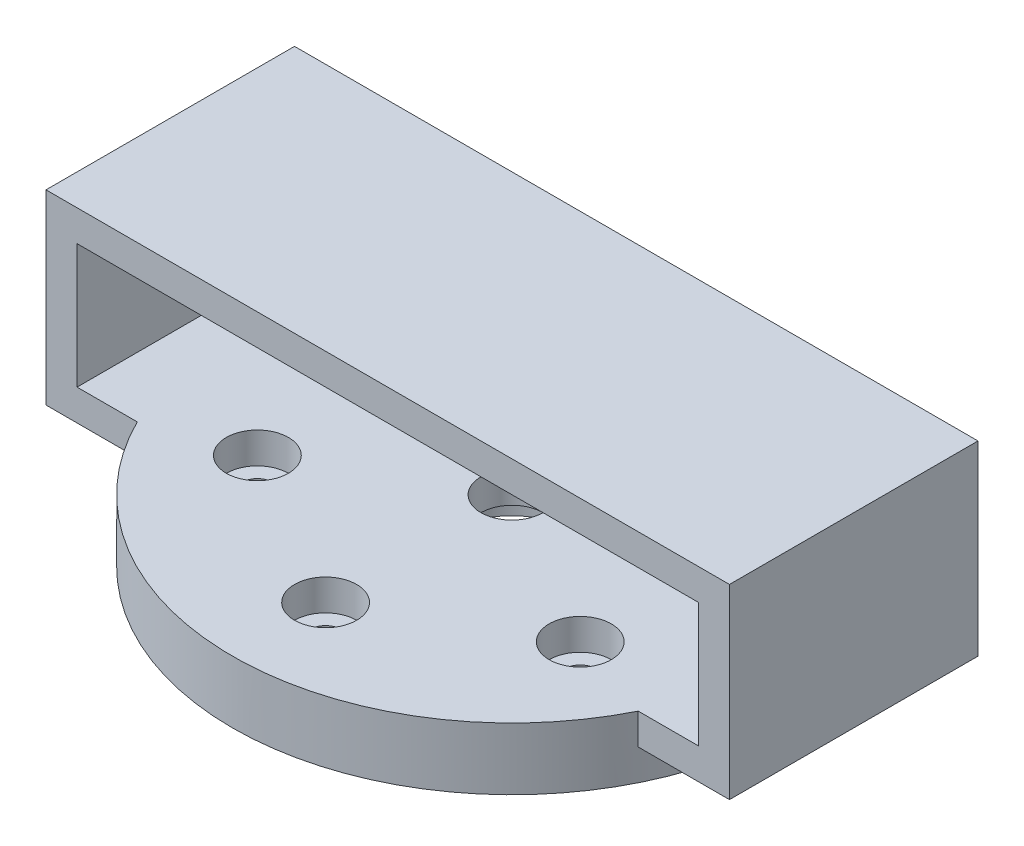
SolidWorks part; units mm, degrees
ref_plane "Front Plane" through (0, 0, 0) normal (0, 0, 1) x (1, 0, 0)
ref_plane "Top Plane" through (0, 0, 0) normal (0, 1, 0) x (1, 0, 0)
ref_plane "Right Plane" through (0, 0, 0) normal (1, 0, 0) x (0, 0, -1)
sketch "Sketch1" plane through (0, 0, 0) normal (0, 1, 0) x (1, 0, 0)
  circle A0 centre (0, 0) radius 45
  circle A2 centre (0, 30) radius 2.5
  circle A3 centre (25.9808, 15) radius 2.5
  circle A4 centre (25.9808, -15) radius 2.5
  circle A5 centre (0, -30) radius 2.5
  circle A6 centre (-25.9808, -15) radius 2.5
  circle A7 centre (-25.9808, 15) radius 2.5
  circle A8 centre (0, 0) radius 10
  point P19 (0, 0)
  dimension "D1" = 90
  dimension "D2" = 20
  dimension "D3" = 5
  dimension "D4" = 30
  dimension "D5" = 6
extrude "Boss-Extrude1" add sketch "Sketch1" along normal blind 10
sketch "Sketch2" plane through (0, 10, 0) normal (0, 1, 0) x (1, 0, 0)
  line L1 (-55, 20) -> (55, 20)
  line L2 (-55, 20) -> (-55, -20)
  line L3 (-55, -20) -> (55, -20)
  line L4 (55, 20) -> (55, -20)
  point P4 (0, -20)
  point P6 (-55, 0)
  dimension "D1" = 110
  dimension "D2" = 40
extrude "Boss-Extrude2" add sketch "Sketch2" along normal blind 25 and the other way blind 5
sketch "Sketch3" plane through (0, 0, -20) normal (0, 0, -1) x (-1, 0, 0)
  line L0 (-55, 35) -> (55, 35) construction
  line L1 (-50, 30) -> (50, 30)
  line L2 (-50, 30) -> (-50, 10)
  line L3 (-50, 10) -> (50, 10)
  line L4 (50, 30) -> (50, 10)
  point P4 (0, 30)
  dimension "D1" = 100
  dimension "D2" = 20
  dimension "D3" = 5
extrude "Cut-Extrude1" cut sketch "Sketch3" against normal blind 45
sketch "Sketch4" plane through (0, 10, 0) normal (0, 1, 0) x (1, 0, 0)
  circle A0 centre (0, 30) radius 5
  circle A1 centre (0, 30) radius 2.5 construction
  circle A2 centre (25.9808, 15) radius 5
  circle A3 centre (25.9808, -15) radius 5
  circle A4 centre (0, -30) radius 5
  circle A5 centre (-25.9808, -15) radius 5
  circle A6 centre (-25.9808, 15) radius 5
  circle A7 centre (0, 0) radius 5
  point P16 (0, 0)
  dimension "D1" = 10
  dimension "D3" = 10
  dimension "D2" = 6
extrude "Cut-Extrude2" cut sketch "Sketch4" against normal blind 5
